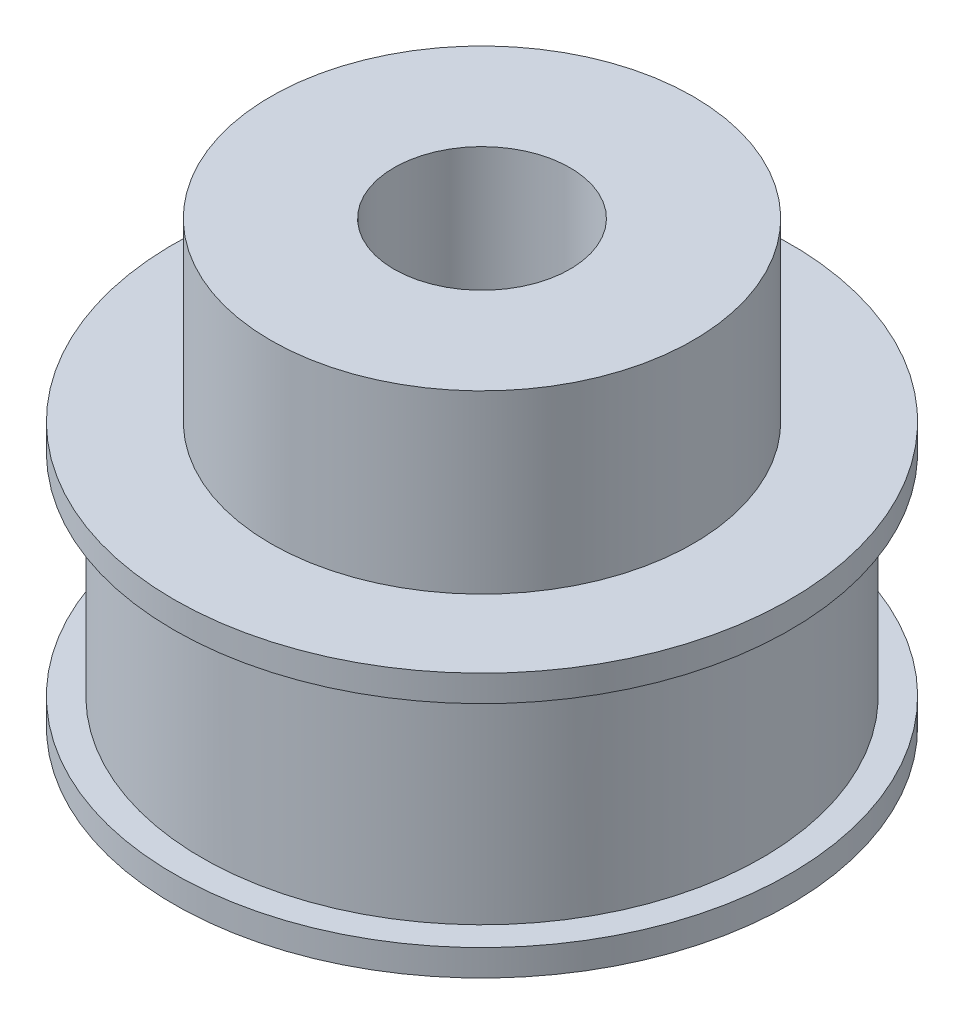
SolidWorks part; units mm, degrees
material "4032-T6"
ref_plane "Front Plane" through (0, 0, 0) normal (0, 0, 1) x (1, 0, 0)
ref_plane "Top Plane" through (0, 0, 0) normal (0, 1, 0) x (1, 0, 0)
ref_plane "Right Plane" through (0, 0, 0) normal (1, 0, 0) x (0, 0, -1)
sketch "Sketch1" plane through (0, 0, 0) normal (0, 1, 0) x (1, 0, 0)
  circle A0 centre (0, 0) radius 32.34
  dimension "D1" = 64.68
extrude "Boss-Extrude1" add sketch "Sketch1" along normal blind 15
sketch "Sketch2" plane through (0, 15, 0) normal (0, 1, 0) x (1, 0, 0)
  circle A0 centre (0, 0) radius 12
  dimension "D1" = 24
extrude "Boss-Extrude2" add sketch "Sketch2" along normal blind 10
sketch "Sketch3" plane through (0, 25, 0) normal (0, 1, 0) x (1, 0, 0)
  circle A0 centre (0, 0) radius 5
  dimension "D1" = 10
extrude "Cut-Extrude1" cut sketch "Sketch3" against normal blind 26
sketch "Sketch4" plane through (0, 0, 0) normal (0, -1, 0) x (1, 0, 0)
  circle A0 centre (0, 0) radius 15.915
  circle A2 centre (0, 0) radius 32.34
  circle A3 centre (0, 0) radius 32.34
  dimension "D1" = 31.83
  dimension "D2" = 0
extrude "Cut-Extrude3" cut sketch "Sketch4" against normal blind 15
sketch "Sketch5" plane through (0, 0, 0) normal (0, -1, 0) x (1, 0, 0)
  circle A0 centre (0, 0) radius 17.5
  circle A1 centre (0, 0) radius 15.915 construction
  circle A2 centre (0, 0) radius 15.915
  dimension "D1" = 35
extrude "Boss-Extrude3" add sketch "Sketch5" against normal blind 1.5
sketch "Sketch6" plane through (0, 15, 0) normal (0, 1, 0) x (1, 0, 0)
  circle A0 centre (0, 0) radius 17.5
  circle A1 centre (0, 0) radius 15.915 construction
  circle A2 centre (0, 0) radius 15.915
  dimension "D1" = 35
extrude "Boss-Extrude4" add sketch "Sketch6" against normal blind 1.5
